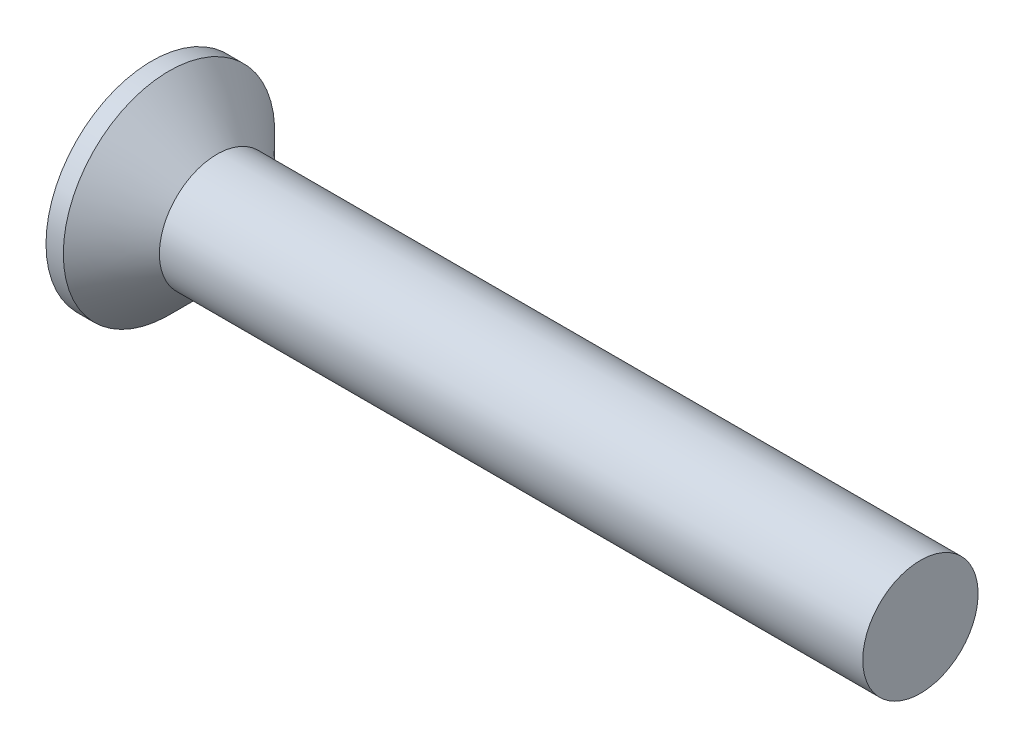
SolidWorks part; units mm, degrees
revolve "Base-Revolve" add sketch "BodySke" angle 360 about L5
sketch "BodySke" plane through (0, 0, 0) normal (0, 0, 1) x (1, 0, 0)
  line L0 (0, 0) -> (0, 2.75)
  line L1 (0, 2.75) -> (0.45, 2.75)
  line L2 (1.7, 1.5) -> (20, 1.5)
  line L3 (20, 1.5) -> (20, 0)
  line L4 (20, 0) -> (0, 0)
  line L5 (-6.35, 0) -> (82.55, 0) construction
  line L6 (1.7, -1.5) -> (20, -1.5) construction
  line L7 (0.45, -2.75) -> (1.7, -1.5) construction
  line L8 (0.45, 2.75) -> (1.7, 1.5)
  line L9 (0, -2.75) -> (0.45, -2.75) construction
  line L10 (2.2, 3.0875) -> (2.2, -6.4375) construction
  line L11 (0, 6.35) -> (0, -3.175) construction
  dimension "Diameter" = 3
  dimension "Length" = 20
  dimension "Head_ht" = 1.7
  dimension "Head_dia" = 5.5
  dimension "Head_ang" = 90
  dimension "D6" = 0.45
  dimension "Advance" = 0.5
  dimension "Thread_nom" = 20
cosmetic thread "ThreadCosmetic" parameters "Thread_length"=17.8, "Thread_minor"=2.439
extrude "Slot" [suppressed] cut sketch "Sketch2" against normal blind 0.9
sketch "Sketch2" plane through (0, 0, 0) normal (-1, 0, 0) x (0, 0, 1)
  line L0 (-2.75, -0.5) -> (2.75, -0.5)
  line L1 (-2.75, -0.5) -> (-2.75, 0.5)
  line L2 (2.75, 0.5) -> (-2.75, 0.5)
  line L3 (2.75, 0.5) -> (2.75, -0.5)
  dimension "Slot_width" = 1
  dimension "D1" = 0.5
  dimension "D2" = 5.5
  dimension "D3" = 2.75
ref_plane "Plane1" through (0, 0, 0) normal (0, 0, 1) x (1, 0, 0)
ref_plane "Plane2" through (0, 0, 0) normal (0, 1, 0) x (1, 0, 0)
ref_plane "Plane3" through (0, 0, 0) normal (1, 0, 0) x (0, 0, -1)
sketch "Sketch3" plane through (0, 0, 0) normal (-1, 0, 0) x (0, 0, 1)
  line L0 (-0.395, 1.55) -> (0.395, 1.55)
  line L1 (0.395, 1.55) -> (0.395, -1.55)
  line L2 (0.395, -1.55) -> (-0.395, -1.55)
  line L3 (-0.395, -1.55) -> (-0.395, 1.55)
  dimension "Cross_dia" = 3.1
  dimension "Cross_width" = 0.79
  dimension "D1" = 1.55
  dimension "D2" = 0.395
ref_plane "Plane4" through (2.08, 0, 0) normal (-1, 0, 0) x (0, 0, 1)
sketch "Sketch4" plane through (2.08, 0, 0) normal (-1, 0, 0) x (0, 0, 1)
  line L0 (-0.1975, 0.1975) -> (0.1975, 0.1975)
  line L3 (0.1975, 0.1975) -> (0.1975, -0.1975)
  line L4 (0.1975, -0.1975) -> (-0.1975, -0.1975)
  line L5 (-0.1975, -0.1975) -> (-0.1975, 0.1975)
  dimension "D2" = 0.395
  dimension "D1" = 0.395
  dimension "D3" = 0.1975
  dimension "D4" = 0.1975
loft "Cross" cut profiles "Sketch3", "Sketch4"
pattern_circular "CirPattern1" count 2 every 90 about axis through (0, 0, 0) along (1, 0, 0) of "Cross"
sketch "ThdSchSke" plane through (0, 0, 0) normal (0, 0, 1) x (1, 0, 0)
  line L0 (2.2, -1.2195) -> (2.0036, -1.5)
  line L1 (2.2, -1.2195) -> (2.3964, -1.5)
  line L2 (2.3964, -1.5) -> (2.3964, -1.875)
  line L3 (-3.175, 0) -> (5.1513, 0) construction
  line L5 (2.3964, -1.875) -> (2.0036, -1.875)
  line L6 (2.0036, -1.875) -> (2.0036, -1.5)
  line L7 (0, 2.75) -> (0, -2.75) construction
  dimension "Diameter" = 3
  dimension "Thread_minor" = 2.439
  dimension "Start" = 2.2
revolve "ThreadSchematic" [suppressed] cut sketch "ThdSchSke" angle 360 about L3
pattern_linear "ThdSchPat" [suppressed]
equation "\"D1@Sketch3\" = \"Cross_dia@Sketch3\" / 2"
equation "\"D2@Sketch3\" = \"Cross_width@Sketch3\" / 2"
equation "\"D1@Sketch4\" = \"Cross_width@Sketch3\" *.5"
equation "\"D2@Sketch4\" = \"D1@Sketch4\""
equation "\"D4@Sketch4\" = \"D2@Sketch4\" / 2"
equation "\"D3@Sketch4\" = \"D1@Sketch4\" / 2"
equation "\"D1@Sketch2\" = \"Slot_width@Sketch2\" / 2"
equation "\"D2@Sketch2\" = \"Head_dia@BodySke\""
equation "\"D3@Sketch2\" = \"D2@Sketch2\" / 2"
equation "\"Thread_length@ThreadCosmetic\" = ((sgn( (\"Length@BodySke\" - \"Advance@BodySke\" - \"Head_ht@BodySke\" ) - \"Thread_nom@BodySke\" )-1)*( (\"Length@BodySke\" - \"Advance@BodySke\" - \"Head_ht@BodySke\" ) - \"Thread_nom@BodySke\" ))/-2+ \"Thread_nom@BodySke\""
equation "\"Thread_minor@ThdSchSke\" = \"Thread_minor@ThreadCosmetic\""
equation "\"Diameter@ThdSchSke\" = \"Diameter@BodySke\""
equation "\"Overcut@ThdSchSke\" = \"Diameter@BodySke\" * 1.25"
equation "\"Start@ThdSchSke\" = 0.000001 + \"Length@BodySke\" - \"Thread_length@ThreadCosmetic\"  '---Countersunk---"
equation "\"Num_threads@ThdSchPat\" = int( \"Thread_length@ThreadCosmetic\" / \"Advance@BodySke\" + 0.999 )  + 1"
equation "\"Advance@ThdSchPat\" = \"Thread_length@ThreadCosmetic\" /  (\"Num_threads@ThdSchPat\" - 1) 'relax it"
